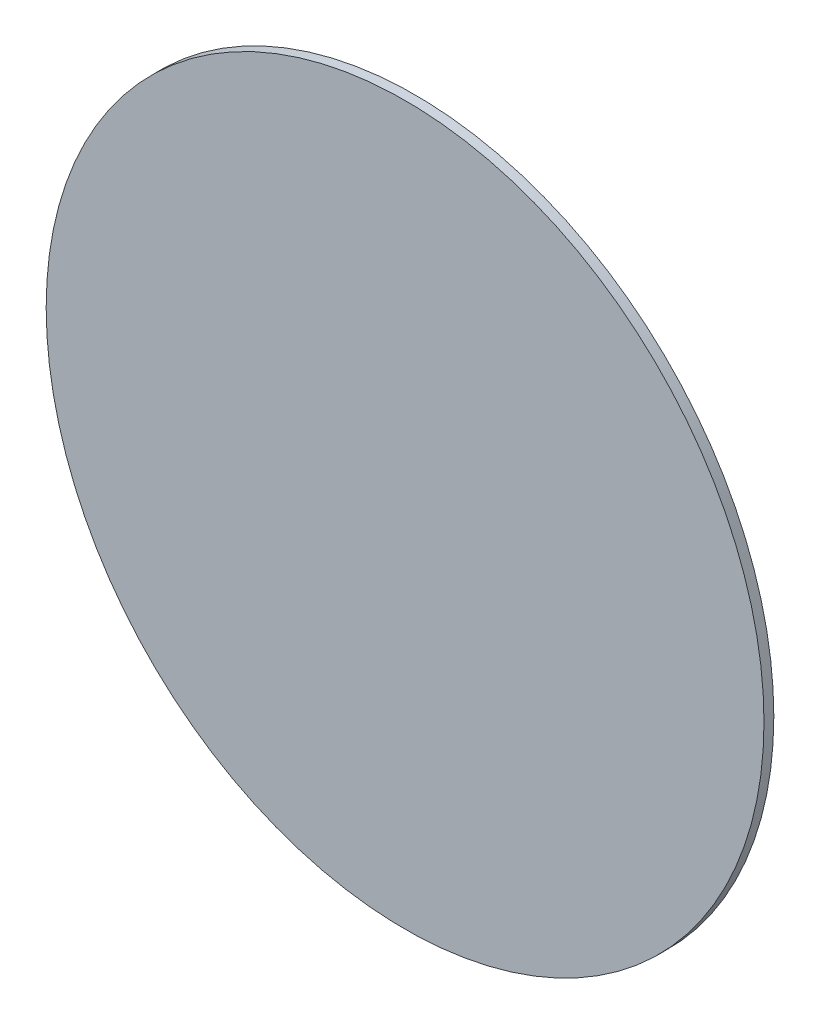
SolidWorks part; units mm, degrees
ref_plane "Front" through (0, 0, 0) normal (0, 0, 1) x (1, 0, 0)
ref_plane "Top" through (0, 0, 0) normal (0, 1, 0) x (1, 0, 0)
ref_plane "Right" through (0, 0, 0) normal (1, 0, 0) x (0, 0, -1)
sketch "Sketch1" plane through (0, 0, 0) normal (0, 0, 1) x (1, 0, 0)
  circle A0 centre (0, 33.3375) radius 115.8875
  circle A1 centre (0, 33.3375) radius 3.175 construction
  dimension "D1" = 231.775
extrude "Extrude1" add sketch "Sketch1" along normal blind 3.175 from offset 19.05
